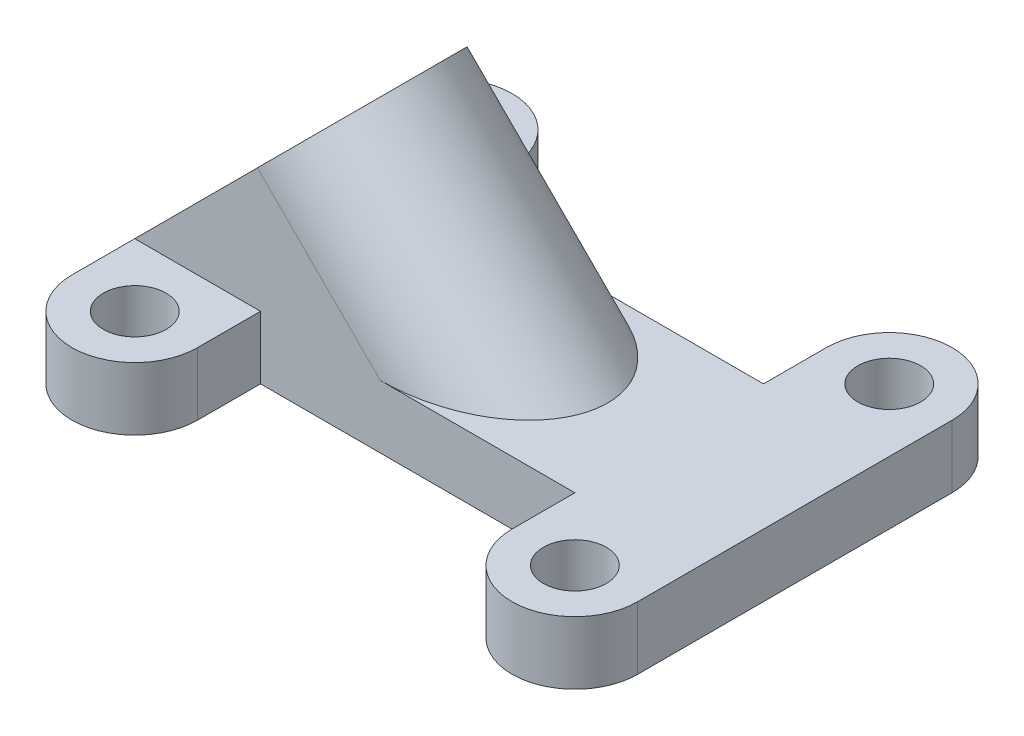
SolidWorks part; units mm, degrees
ref_plane "前基準面" through (0, 0, 0) normal (0, 0, 1) x (1, 0, 0)
ref_plane "上基準面" through (0, 0, 0) normal (0, 1, 0) x (1, 0, 0)
ref_plane "右基準面" through (0, 0, 0) normal (1, 0, 0) x (0, 0, -1)
sketch "草圖1" plane through (0, 0, 0) normal (0, 1, 0) x (1, 0, 0)
  line L0 (-28.3451, 0) -> (51.6373, 0) construction
  line L1 (-17.5, -12.5) -> (-17.5, 12.5) construction
  line L2 (-22.5, -12.5) -> (-22.5, 12.5) construction
  line L3 (-12.5, -12.5) -> (-12.5, 12.5) construction
  line L4 (0, 27.9754) -> (0, -32.9049) construction
  line L5 (17.5, -12.5) -> (17.5, 12.5) construction
  line L6 (22.5, -12.5) -> (22.5, 12.5) construction
  line L7 (12.5, -12.5) -> (12.5, 12.5) construction
  line L8 (-12.5, 7.5) -> (12.5, 7.5)
  line L9 (-12.5, -7.5) -> (12.5, -7.5)
  line L10 (-22.5, 12.5) -> (-22.5, -12.5)
  line L11 (-12.5, 7.5) -> (-12.5, 12.5)
  line L12 (22.5, 12.5) -> (22.5, -12.5)
  line L13 (12.5, 7.5) -> (12.5, 12.5)
  line L14 (-12.5, -7.5) -> (-12.5, -12.5)
  line L15 (12.5, -7.5) -> (12.5, -12.5)
  arc A0 (-22.5, -12.5) -> (-12.5, -12.5) centre (-17.5, -12.5) ccw construction
  arc A1 (-12.5, 12.5) -> (-22.5, 12.5) centre (-17.5, 12.5) ccw construction
  arc A2 (22.5, -12.5) -> (12.5, -12.5) centre (17.5, -12.5) cw construction
  arc A3 (12.5, 12.5) -> (22.5, 12.5) centre (17.5, 12.5) cw construction
  circle A4 centre (-17.5, -12.5) radius 2.5
  circle A5 centre (-17.5, 12.5) radius 2.5
  circle A6 centre (17.5, -12.5) radius 2.5
  circle A7 centre (17.5, 12.5) radius 2.5
  arc A8 (-22.5, 12.5) -> (-12.5, 12.5) centre (-17.5, 12.5) cw
  arc A9 (-22.5, -12.5) -> (-12.5, -12.5) centre (-17.5, -12.5) ccw
  arc A10 (22.5, -12.5) -> (12.5, -12.5) centre (17.5, -12.5) cw
  arc A11 (12.5, 12.5) -> (22.5, 12.5) centre (17.5, 12.5) cw
  point P5 (-17.5, 0)
  point P14 (17.5, 0)
  dimension "D3" = 5
  dimension "D4" = 5
  dimension "D1" = 35
  dimension "D2" = 25
  dimension "D5" = 15
extrude "填料-伸長1" add sketch "草圖1" along normal blind 5
sketch "草圖4" plane through (0, 0, 0) normal (0, 0, 1) x (1, 0, 0)
  line L0 (2.0161, 0) -> (-13.9481, 15.9643) construction
  line L1 (-12.5, 0) -> (12.5, 0) construction
  line L2 (-22.5, 0) -> (-12.5, 0) construction
  dimension "D1" = 45
  dimension "D2" = 13.8
ref_plane "平面2" through (-13.75, 13.75, 0) normal (-0.7071, 0.7071, 0) x (0, 0, 1)
sketch "草圖6" plane through (-13.75, 13.75, 0) normal (-0.7071, 0.7071, 0) x (0, 0, 1)
  line L0 (-7.5, -12.3744) -> (-7.5, 1.4256)
  line L1 (-12.5, -12.3744) -> (12.5, -12.3744) construction
  line L2 (-7.5, -12.3744) -> (7.5, -12.3744)
  line L3 (7.5, 1.4256) -> (7.5, -12.3744)
  line L4 (0, 5.9328) -> (0, -16.9507) construction
  line L5 (-7.5, 12.3744) -> (-7.5, -5.3033) construction
  arc A0 (-7.5, 1.4256) -> (7.5, 1.4256) centre (0, 1.4256) cw
  circle A1 centre (0, 1.4256) radius 3
  dimension "D1" = 6
extrude "填料-伸長3" add sketch "草圖6" against normal up to surface (20.8711 mm away)
sketch "草圖9" plane through (-13.75, 13.75, 0) normal (-0.7071, 0.7071, 0) x (0, 0, 1)
  circle A1 centre (0, 1.4256) radius 3 construction
  circle A2 centre (0, 1.4256) radius 3
extrude "除料-伸長2" cut sketch "草圖9" against normal through all
